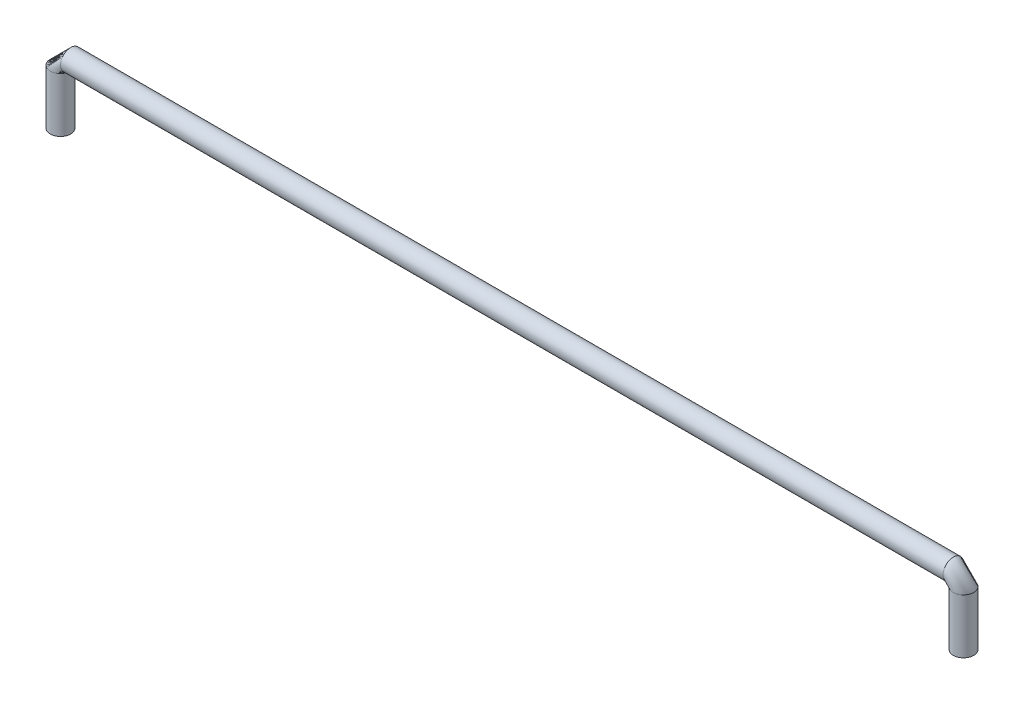
SolidWorks part; units mm, degrees
material "Alloy Steel"
ref_plane "Front Plane" through (0, 0, 0) normal (0, 0, 1) x (1, 0, 0)
ref_plane "Top Plane" through (0, 0, 0) normal (0, 1, 0) x (1, 0, 0)
ref_plane "Right Plane" through (0, 0, 0) normal (1, 0, 0) x (0, 0, -1)
sketch "Sketch1" plane through (0, 0, 0) normal (0, 0, 1) x (1, 0, 0)
  line L0 (65.786, 0) -> (-65.786, 0)
  line L1 (-67.31, -1.524) -> (-67.31, -9.652)
  line L2 (67.31, -1.524) -> (67.31, -9.652)
  arc A0 (65.786, 0) -> (67.31, -1.524) centre (65.786, -1.524) cw
  arc A1 (-65.786, 0) -> (-67.31, -1.524) centre (-65.786, -1.524) ccw
  point P7 (67.31, 0)
  point P10 (-67.31, 0)
  dimension "D3" = 1.524
  dimension "D1" = 134.62
  dimension "D2" = 9.652
ref_plane "Plane3" through (0, -9.652, 0) normal (0, 1, 0) x (-1, 0, 0)
sketch "Sketch5" plane through (0, -9.652, 0) normal (0, 1, 0) x (-1, 0, 0)
  circle A0 centre (67.31, 0) radius 1.524
  dimension "D1" = 3.048
sweep "Sweep1" add profiles "Sketch5" path "Sketch1"
